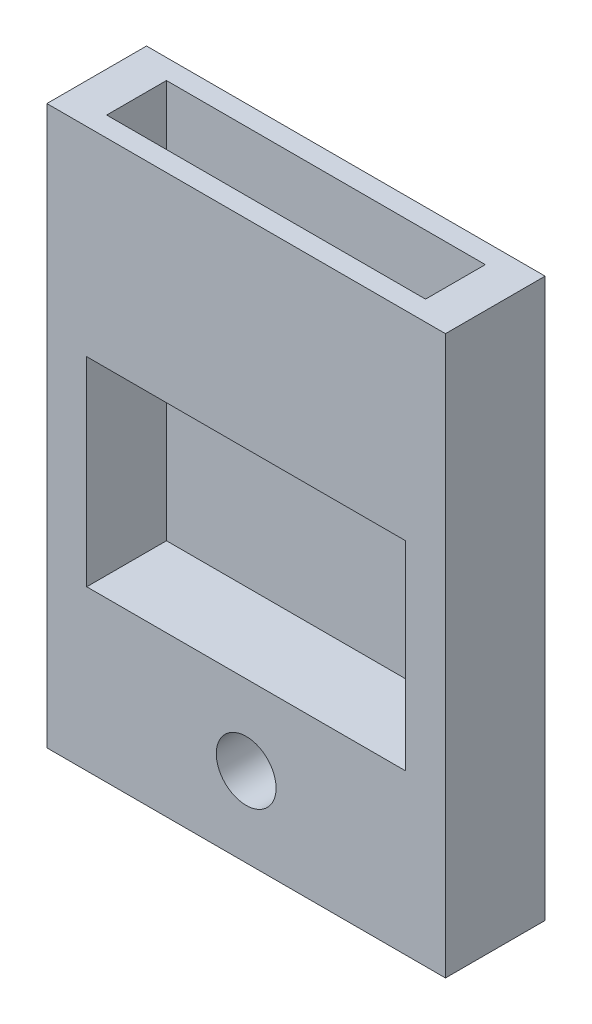
SolidWorks part; units mm, degrees
ref_plane "Front Plane" through (0, 0, 0) normal (0, 0, 1) x (1, 0, 0)
ref_plane "Top Plane" through (0, 0, 0) normal (0, 1, 0) x (1, 0, 0)
ref_plane "Right Plane" through (0, 0, 0) normal (1, 0, 0) x (0, 0, -1)
sketch "Sketch1" plane through (0, 0, 0) normal (0, 0, 1) x (1, 0, 0)
  line L1 (0, 0) -> (20, 0)
  line L2 (0, 0) -> (0, 28)
  line L3 (0, 28) -> (20, 28)
  line L4 (20, 0) -> (20, 28)
  dimension "D1" = 20
  dimension "D2" = 28
extrude "Boss-Extrude1" add sketch "Sketch1" along normal blind 5
sketch "Sketch2" plane through (0, 0, 5) normal (0, 0, 1) x (1, 0, 0)
  line L0 (10, 28) -> (10, 0) construction
  line L1 (20, 28) -> (0, 28) construction
  line L2 (0, 0) -> (20, 0) construction
  circle A0 centre (10, 4) radius 1.5
  point P8 (13, 3.2605)
  dimension "D1" = 3
  dimension "D2" = 4
extrude "Cut-Extrude1" cut sketch "Sketch2" against normal blind 5
sketch "Sketch3" plane through (0, 28, 0) normal (0, 1, 0) x (1, 0, 0)
  line L0 (10, 0) -> (10, -5) construction
  line L5 (20, 0) -> (0, 0) construction
  line L6 (20, -5) -> (0, -5) construction
  line L7 (0, -2.5) -> (20, -2.5) construction
  line L8 (0, -5) -> (0, 0) construction
  line L9 (20, -5) -> (20, 0) construction
  line L11 (2, -4) -> (18, -4)
  line L12 (2, -4) -> (2, -1)
  line L13 (2, -1) -> (18, -1)
  line L14 (18, -4) -> (18, -1)
  line L15 (2, -4) -> (18, -1) construction
  line L16 (2, -1) -> (18, -4) construction
  point P0 (10, -2.5)
  dimension "D1" = 16
  dimension "D2" = 3
extrude "Cut-Extrude2" cut sketch "Sketch3" against normal blind 20
sketch "Sketch4" plane through (0, 0, 5) normal (0, 0, 1) x (1, 0, 0)
  line L1 (2, 18) -> (18, 18)
  line L2 (2, 18) -> (2, 8)
  line L3 (2, 8) -> (18, 8)
  line L4 (18, 18) -> (18, 8)
  line L5 (10, 0) -> (10, 36) construction
  line L6 (0, 0) -> (20, 0) construction
  line L7 (20, 28) -> (0, 28) construction
  point P10 (10, 18)
  dimension "D1" = 16
  dimension "D2" = 10
  dimension "D3" = 20
extrude "Cut-Extrude3" cut sketch "Sketch4" against normal blind 4
